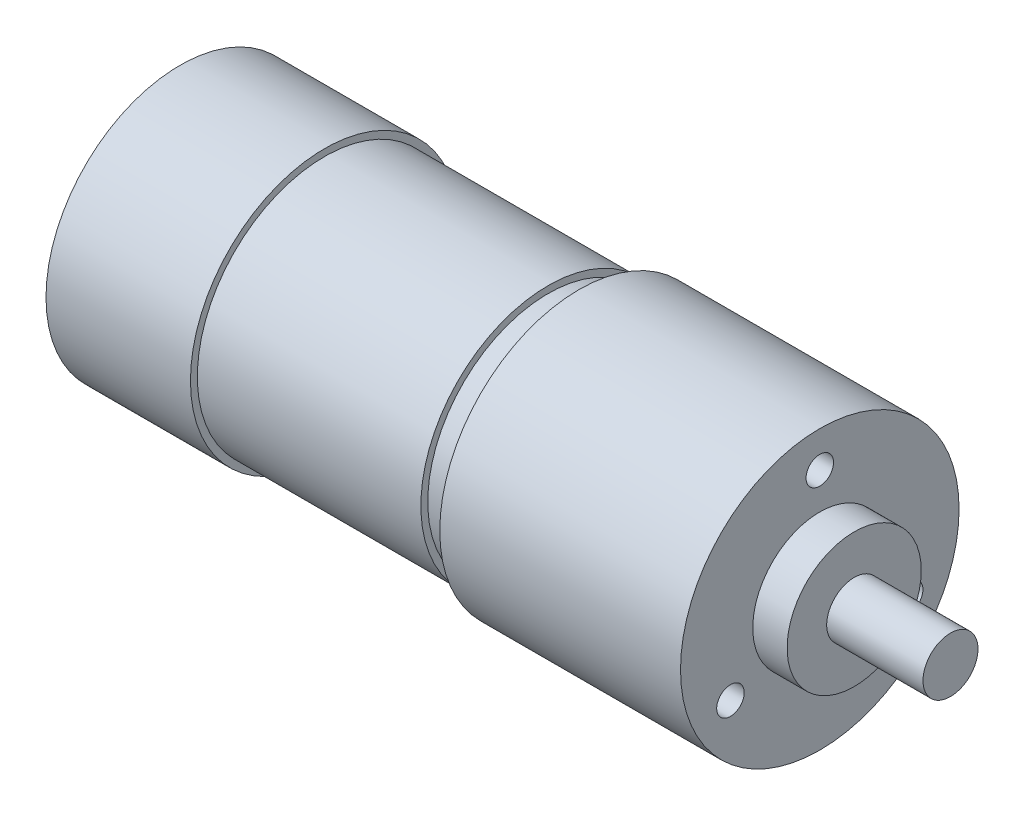
SolidWorks part; units mm, degrees
material "1.0035 (S185)"
ref_plane "Piano frontale" through (0, 0, 0) normal (0, 0, 1) x (1, 0, 0)
ref_plane "Piano superiore" through (0, 0, 0) normal (0, 1, 0) x (1, 0, 0)
ref_plane "Piano destro" through (0, 0, 0) normal (1, 0, 0) x (0, 0, -1)
sketch "Schizzo3" plane through (0, 0, 0) normal (0, 1, 0) x (1, 0, 0)
  line L0 (0, 0) -> (0, 19.5)
  line L1 (0, 19.5) -> (21, 19.5)
  line L2 (21, 18.5) -> (53.5, 18.5)
  line L3 (53.5, 18.5) -> (53.5, 17.5)
  line L4 (53.5, 17.5) -> (58, 17.5)
  line L5 (58, 20.25) -> (93, 20.25)
  line L6 (93, 20.25) -> (93, 9.75)
  line L7 (93, 9.75) -> (98, 9.75)
  line L8 (98, 9.75) -> (98, 4)
  line L9 (98, 4) -> (112, 4)
  line L10 (112, 4) -> (112, 0)
  line L11 (112, 0) -> (0, 0)
  line L12 (21, 18.5) -> (21, 19.5)
  line L13 (58, 17.5) -> (58, 20.25)
  dimension "D1" = 19.5
  dimension "D2" = 93
  dimension "D3" = 21
  dimension "D4" = 4
  dimension "D5" = 14
  dimension "D6" = 5
  dimension "D7" = 4.5
  dimension "D8" = 35
  dimension "D9" = 1
  dimension "D10" = 1
  dimension "D11" = 20.25
  dimension "D12" = 9.75
revolve "Rivoluzione1" add sketch "Schizzo3" angle 360 about L11
sketch "Schizzo4" plane through (93, 0, 0) normal (1, 0, 0) x (0, 0, -1)
  line L0 (0, 0) -> (30.9291, -17.8569) construction
  line L1 (0, 0) -> (-30.9291, -17.8569) construction
  line L2 (0, 0) -> (0, 35.7138) construction
  line L3 (0, 22.275) -> (0, -22.275) construction
  circle A0 centre (0, 15) radius 2
  circle A1 centre (12.9904, -7.5) radius 2
  circle A2 centre (-12.9904, -7.5) radius 2
  circle A3 centre (0, 0) radius 15 construction
  point P12 (-12.9904, -7.5)
  point P13 (0, 15)
  point P14 (12.9904, -7.5)
  dimension "D1" = 4
  dimension "D2" = 30
  dimension "D3" = 120
  dimension "D4" = 120
extrude "Taglio-Estrusione1" cut sketch "Schizzo4" against normal blind 8
